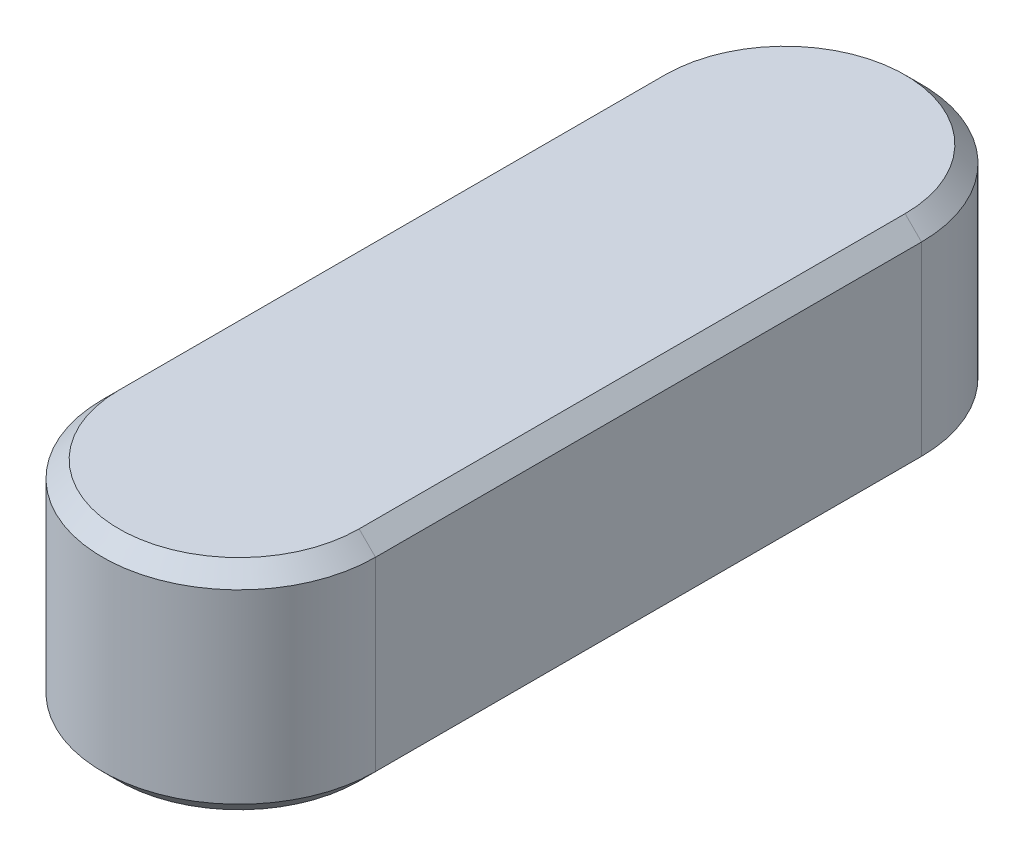
SolidWorks part; units mm, degrees
material "AISI 4340 Steel, normalized"
ref_plane "Front Plane" through (0, 0, 0) normal (0, 0, 1) x (1, 0, 0)
ref_plane "Top Plane" through (0, 0, 0) normal (0, 1, 0) x (1, 0, 0)
ref_plane "Right Plane" through (0, 0, 0) normal (1, 0, 0) x (0, 0, -1)
sketch "Sketch1" plane through (0, 0, 0) normal (0, 1, 0) x (1, 0, 0)
  line L0 (0, 0) -> (0, 20) construction
  line L1 (5, 0) -> (5, 20)
  line L2 (-5, 0) -> (-5, 20)
  arc A0 (5, 0) -> (-5, 0) centre (0, 0) cw
  arc A1 (5, 20) -> (-5, 20) centre (0, 20) ccw
  dimension "D1" = 20
  dimension "D2" = 5
  dimension "D3" = 5
extrude "Boss-Extrude1" add sketch "Sketch1" along normal blind 8
chamfer "Chamfer1" distance 0.6 8 edges at (-5, 8, -10) (0, 8, 5) (0, 8, -25) (5, 8, -10) (-5, 0, -10) (0, 0, 5) (0, 0, -25) (5, 0, -10)
